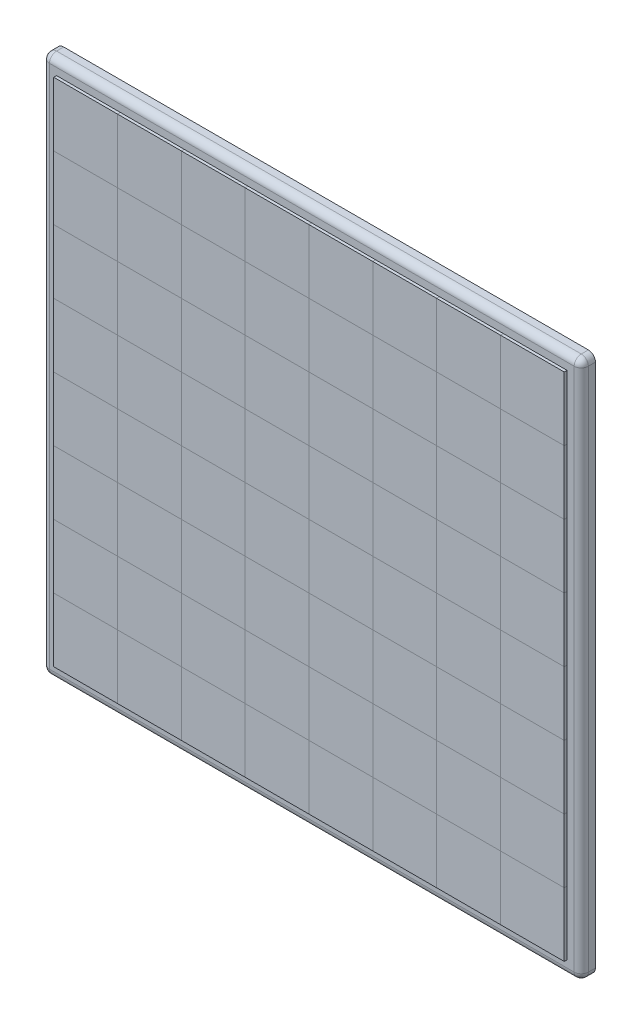
SolidWorks part; units mm, degrees
ref_plane "Front Plane" through (0, 0, 0) normal (0, 0, 1) x (1, 0, 0)
ref_plane "Top Plane" through (0, 0, 0) normal (0, 1, 0) x (1, 0, 0)
ref_plane "Right Plane" through (0, 0, 0) normal (1, 0, 0) x (0, 0, -1)
sketch "Sketch1" plane through (0, 0, 0) normal (0, 0, 1) x (1, 0, 0)
  line L1 (-190, -190) -> (190, -190)
  line L2 (-190, -190) -> (-190, 190)
  line L3 (-190, 190) -> (190, 190)
  line L4 (190, -190) -> (190, 190)
  line L5 (-190, -190) -> (190, 190) construction
  line L6 (-190, 190) -> (190, -190) construction
  point P0 (0, 0)
  dimension "D1" = 380
extrude "Boss-Extrude1" add sketch "Sketch1" along normal blind 10
sketch "Sketch2" plane through (0, 0, 10) normal (0, 0, 1) x (1, 0, 0)
  line L0 (190, 190) -> (-190, 190) construction
  line L1 (-180, 180) -> (-135, 180)
  line L2 (-180, 180) -> (-180, 135)
  line L3 (-180, 135) -> (-135, 135)
  line L4 (-135, 180) -> (-135, 135)
  line L5 (-180, 180) -> (-135, 135) construction
  line L6 (-180, 135) -> (-135, 180) construction
  line L7 (-190, 190) -> (-190, -190) construction
  point P0 (-157.5, 157.5)
  dimension "D1" = 45
  dimension "D2" = 10
  dimension "D3" = 10
extrude "Boss-Extrude2" add sketch "Sketch2" along normal blind 2
pattern_linear "LPattern1" count 4 spacing 90 along (1, 0, 0) count 4 spacing 90 along (0, -1, 0) of "Boss-Extrude2"
sketch "Sketch3" plane through (0, 0, 10) normal (0, 0, 1) x (1, 0, 0)
  line L0 (-90, 180) -> (-90, 135) construction
  line L1 (-135, 180) -> (-90, 180)
  line L2 (-135, 180) -> (-135, 135)
  line L3 (-135, 135) -> (-90, 135)
  line L4 (-90, 180) -> (-90, 135)
  line L5 (-90, 180) -> (-90, 135) construction
extrude "Boss-Extrude4" add sketch "Sketch3" along normal blind 2 separate body
pattern_linear "LPattern2" count 4 spacing 90 along (1, 0, 0) count 4 spacing 90 along (0, -1, 0) of "Boss-Extrude4"
sketch "Sketch4" plane through (0, 0, 10) normal (0, 0, 1) x (1, 0, 0)
  line L1 (-180, 135) -> (-135, 135)
  line L2 (-180, 135) -> (-180, 90)
  line L3 (-180, 90) -> (-135, 90)
  line L4 (-135, 135) -> (-135, 90)
extrude "Boss-Extrude5" add sketch "Sketch4" along normal blind 2 separate body
sketch "Sketch5" plane through (0, 0, 10) normal (0, 0, 1) x (1, 0, 0)
  line L1 (-135, 135) -> (-90, 135)
  line L2 (-135, 135) -> (-135, 90)
  line L3 (-135, 90) -> (-90, 90)
  line L4 (-90, 135) -> (-90, 90)
extrude "Boss-Extrude6" add sketch "Sketch5" along normal blind 2 separate body
pattern_linear "LPattern4" count 4 spacing 90 along (0, -1, 0) count 4 spacing 90 along (1, 0, 0) of "Boss-Extrude5"
pattern_linear "LPattern5" count 4 spacing 90 along (1, 0, 0) count 4 spacing 90 along (0, -1, 0) of "Boss-Extrude6"
fillet "Fillet1" radius 5 8 edges at (-190, 190, 5) (190, 190, 5) (190, -190, 5) (-190, -190, 5) (190, 0, 10) (0, -190, 10) (-190, 0, 10) (0, 190, 10)
